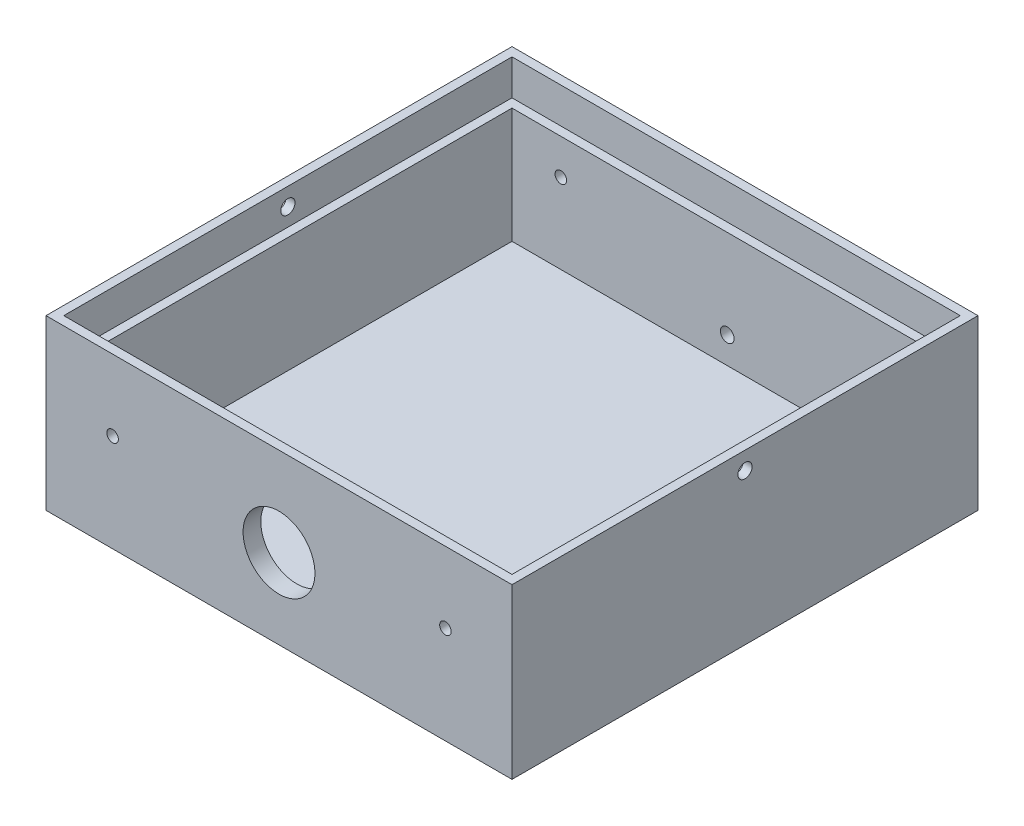
SolidWorks part; units mm, degrees
ref_plane "Front Plane" through (0, 0, 0) normal (0, 0, 1) x (1, 0, 0)
ref_plane "Top Plane" through (0, 0, 0) normal (0, 1, 0) x (1, 0, 0)
ref_plane "Right Plane" through (0, 0, 0) normal (1, 0, 0) x (0, 0, -1)
sketch "Sketch1" plane through (0, 0, 0) normal (0, 1, 0) x (1, 0, 0)
  line L1 (-52.5, 52.5) -> (52.5, 52.5)
  line L2 (-52.5, 52.5) -> (-52.5, -52.5)
  line L3 (-52.5, -52.5) -> (52.5, -52.5)
  line L4 (52.5, 52.5) -> (52.5, -52.5)
  line L5 (-52.5, 52.5) -> (52.5, -52.5) construction
  line L6 (-52.5, -52.5) -> (52.5, 52.5) construction
  point P0 (0, 0)
  dimension "D1" = 105
  dimension "D2" = 105
extrude "Boss-Extrude1" add sketch "Sketch1" along normal blind 38
sketch "Sketch2" plane through (0, 38, 0) normal (0, 1, 0) x (1, 0, 0)
  line L0 (-52.5, 52.5) -> (-52.5, -52.5) construction
  line L1 (-48.5, 48.5) -> (48.5, 48.5)
  line L2 (-48.5, 48.5) -> (-48.5, -48.5)
  line L3 (-48.5, -48.5) -> (48.5, -48.5)
  line L4 (48.5, 48.5) -> (48.5, -48.5)
  line L5 (-48.5, 48.5) -> (48.5, -48.5) construction
  line L6 (-48.5, -48.5) -> (48.5, 48.5) construction
  line L7 (52.5, 52.5) -> (-52.5, 52.5) construction
  point P0 (0, 0)
  dimension "D1" = 4
  dimension "D2" = 4
extrude "Cut-Extrude1" cut sketch "Sketch2" against normal blind 34
sketch "Sketch3" plane through (0, 38, 0) normal (0, 1, 0) x (1, 0, 0)
  line L0 (-52.5, 52.5) -> (-52.5, -52.5) construction
  line L1 (-50.5, 50.5) -> (50.5, 50.5)
  line L2 (-50.5, 50.5) -> (-50.5, -50.5)
  line L3 (-50.5, -50.5) -> (50.5, -50.5)
  line L4 (50.5, 50.5) -> (50.5, -50.5)
  line L5 (-50.5, 50.5) -> (50.5, -50.5) construction
  line L6 (-50.5, -50.5) -> (50.5, 50.5) construction
  line L7 (52.5, 52.5) -> (-52.5, 52.5) construction
  point P0 (0, 0)
  dimension "D1" = 2
  dimension "D2" = 2
extrude "Cut-Extrude2" cut sketch "Sketch3" against normal blind 8
sketch "Sketch5" plane through (52.5, 0, 0) normal (1, 0, 0) x (0, 0, -1)
  line L0 (-52.5, 38) -> (52.5, 38) construction
  circle A0 centre (0, 34) radius 1.6
  dimension "D1" = 3.2
  dimension "D2" = 4
extrude "Cut-Extrude3" cut sketch "Sketch5" against normal through all
sketch "Sketch7" plane through (0, 0, 48.5) normal (0, 0, -1) x (-1, 0, 0)
  line L0 (-48.5, 30) -> (48.5, 30) construction
  circle A0 centre (0, 18) radius 8.1
  dimension "D1" = 16.2
  dimension "D2" = 12
extrude "Cut-Extrude4" cut sketch "Sketch7" against normal up to next
sketch "Sketch10" plane through (0, 0, 0) normal (0, -1, 0) x (1, 0, 0)
  line L1 (5, -10) -> (0, -10)
  line L2 (5, -10) -> (5, 10)
  line L3 (5, 10) -> (0, 10)
  line L5 (0, -7) -> (2, -7)
  line L7 (0, -3) -> (2, -3)
  line L8 (2, -7) -> (2, -3)
  line L9 (0, 3) -> (2, 3)
  line L11 (0, 7) -> (2, 7)
  line L12 (2, 3) -> (2, 7)
  arc A0 (0, 0) -> (0, -10) centre (0, -5) ccw
  arc A1 (0, 10) -> (0, 0) centre (0, 5) ccw
  arc A2 (0, -3) -> (0, -7) centre (0, -5) ccw
  arc A3 (0, 7) -> (0, 3) centre (0, 5) ccw
  dimension "D3" = 10
  dimension "D4" = 10
  dimension "D5" = 4
  dimension "D6" = 4
  dimension "D1" = 5
  dimension "D2" = 20
  dimension "D7" = 4
  dimension "D8" = 2
  dimension "D9" = 2
  dimension "D10" = 4
extrude "Cut-Extrude5" cut sketch "Sketch10" against normal blind 1
sketch "Sketch11" plane through (0, 0, 52.5) normal (0, 0, 1) x (1, 0, 0)
  line L0 (-52.5, 38) -> (-52.5, 0) construction
  line L1 (-52.5, 38) -> (52.5, 38) construction
  line L2 (0, 7.5861) -> (0, 33.6351) construction
  circle A0 centre (-37.5, 22) radius 1.3
  circle A1 centre (37.5, 22) radius 1.3
  dimension "D1" = 2.6
  dimension "D2" = 15
  dimension "D3" = 16
extrude "Cut-Extrude6" cut sketch "Sketch11" against normal through all
sketch "Sketch12" plane through (0, 0, -52.5) normal (0, 0, -1) x (-1, 0, 0)
  line L0 (-52.5, 0) -> (52.5, 0) construction
  circle A0 centre (0, 10) radius 1.55
  dimension "D1" = 3.1
  dimension "D2" = 10
extrude "Cut-Extrude7" cut sketch "Sketch12" against normal up to next
